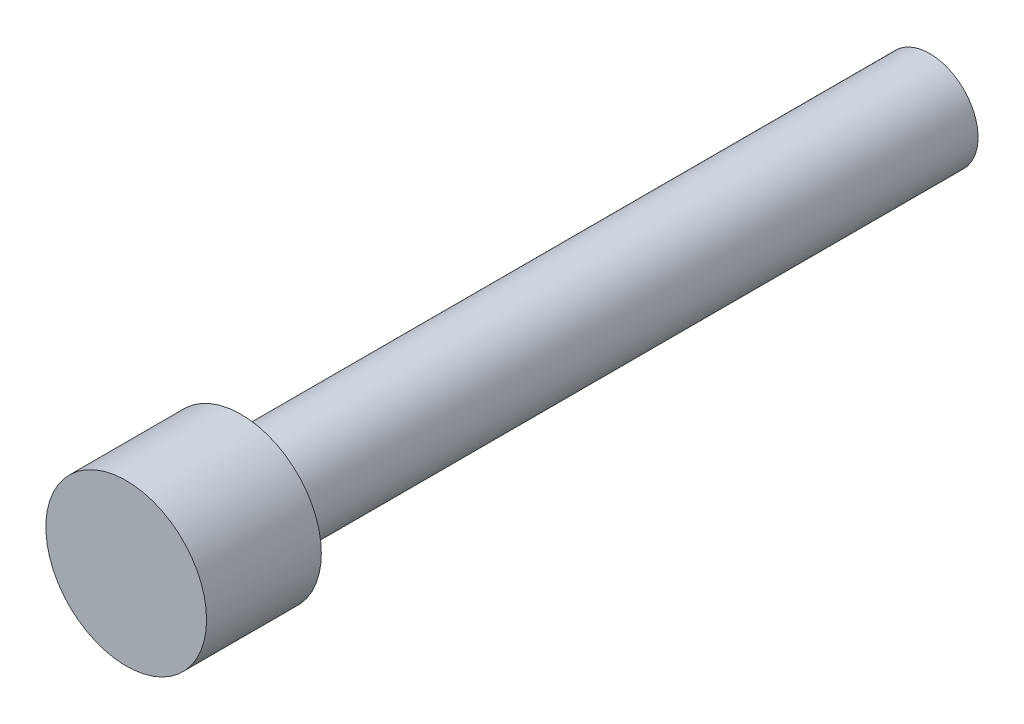
SolidWorks part; units mm, degrees
ref_plane "Front Plane" through (0, 0, 0) normal (0, 0, 1) x (1, 0, 0)
ref_plane "Top Plane" through (0, 0, 0) normal (0, 1, 0) x (1, 0, 0)
ref_plane "Right Plane" through (0, 0, 0) normal (1, 0, 0) x (0, 0, -1)
sketch "Sketch1" plane through (0, 0, 0) normal (0, 0, 1) x (1, 0, 0)
  circle A0 centre (0, 0) radius 1.5875
  dimension "D1" = 3.175
extrude "Boss-Extrude1" add sketch "Sketch1" along normal blind 19.05
sketch "Sketch2" plane through (0, 0, 19.05) normal (0, 0, 1) x (1, 0, 0)
  circle A0 centre (0, 0) radius 2.2225
  dimension "D1" = 4.445
extrude "Boss-Extrude2" add sketch "Sketch2" along normal blind 3.175
other "Move Face1" face at (1.5875, 0, 19.05) parameters "D1"=0.25
